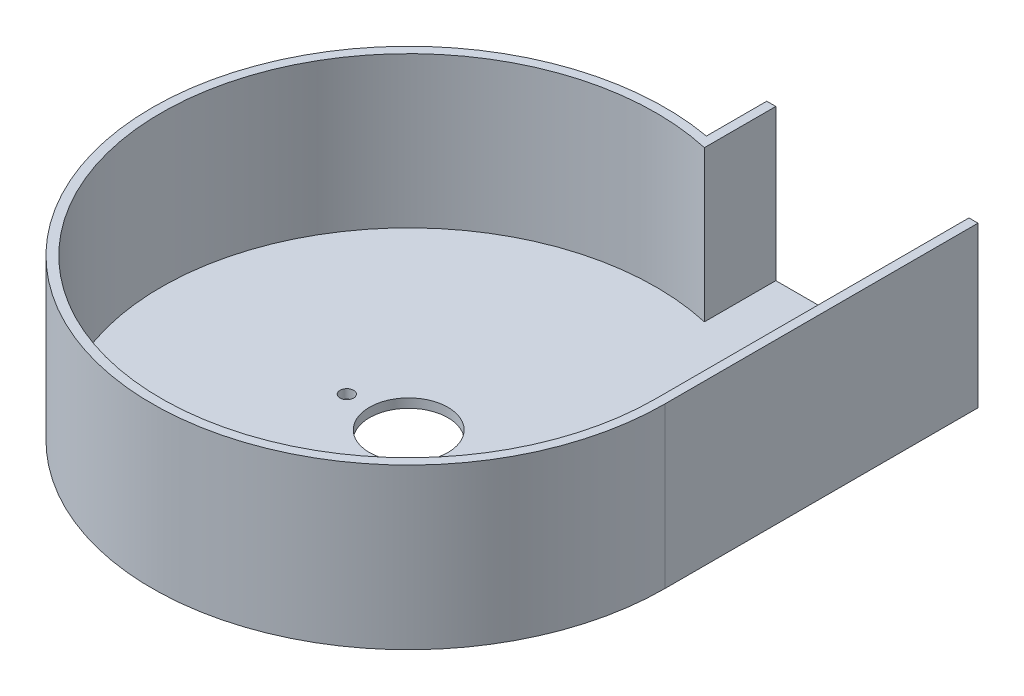
SolidWorks part; units mm, degrees
ref_plane "Front Plane" through (0, 0, 0) normal (0, 0, 1) x (1, 0, 0)
ref_plane "Top Plane" through (0, 0, 0) normal (0, 1, 0) x (1, 0, 0)
ref_plane "Right Plane" through (0, 0, 0) normal (1, 0, 0) x (0, 0, -1)
sketch "Sketch2" plane through (0, 0, 0) normal (0, 1, 0) x (1, 0, 0)
  line L2 (85, 0) -> (85, 103.666)
  line L3 (85, 103.666) -> (15, 103.666)
  line L4 (15, 83.666) -> (15, 103.666)
  circle A0 centre (0, 0) radius 59 construction
  arc A1 (15, 83.666) -> (85, 0) centre (0, 0) ccw
  circle A2 centre (0, 0) radius 20.5 construction
  circle A3 centre (20.5, 0) radius 2.25
  circle A4 centre (-20.5, 0) radius 2.25
  circle A5 centre (0, 0) radius 13
  dimension "D1" = 118
  dimension "D2" = 85
  dimension "D3" = 70
  dimension "D4" = 4.5
  dimension "D6" = 26
  dimension "D5" = 41
  dimension "D7" = 20
extrude "Boss-Extrude1" add sketch "Sketch2" along normal blind 3
sketch "Sketch3" plane through (0, 3, 0) normal (0, 1, 0) x (1, 0, 0)
  line L3 (85, 103.666) -> (15, 103.666) construction
  line L4 (15, 103.666) -> (18, 103.666)
  line L5 (82, 103.666) -> (85, 103.666)
  line L6 (82, 0) -> (82, 100.666)
  line L7 (82, 100.666) -> (18, 100.666)
  line L8 (18, 100.666) -> (18, 80)
  line L9 (82, 0) -> (82, 103.666)
  line L11 (18, 103.666) -> (18, 80)
  line L12 (85, 0) -> (85, 103.666)
  line L13 (85, 103.666) -> (15, 103.666)
  line L14 (15, 103.666) -> (15, 83.666)
  line L15 (85, 0) -> (85, 103.666)
  line L17 (15, 103.666) -> (15, 83.666)
  arc A2 (18, 80) -> (82, 0) centre (0, 0) ccw
  arc A3 (18, 80) -> (82, 0) centre (0, 0) ccw
  arc A4 (15, 83.666) -> (85, 0) centre (0, 0) ccw
  arc A5 (15, 83.666) -> (85, 0) centre (0, 0) ccw
  dimension "D1" = 3
  dimension "D2" = 0
extrude "Boss-Extrude2" add sketch "Sketch3" along normal blind 50
